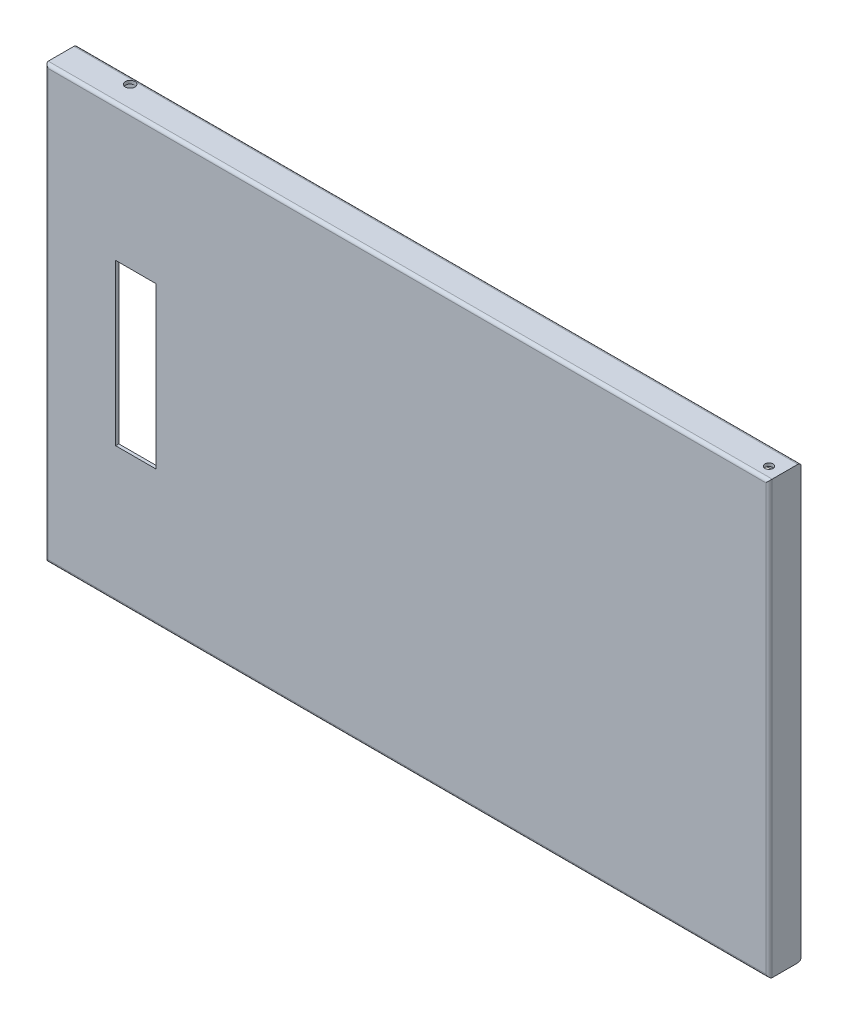
SolidWorks part; units mm, degrees
ref_plane "Front Plane" through (0, 0, 0) normal (0, 0, 1) x (1, 0, 0)
ref_plane "Top Plane" through (0, 0, 0) normal (0, 1, 0) x (1, 0, 0)
ref_plane "Right Plane" through (0, 0, 0) normal (1, 0, 0) x (0, 0, -1)
sketch "Sketch1" plane through (0, 0, 0) normal (0, 0, 1) x (1, 0, 0)
  line L1 (-225.5, 134.5) -> (225.5, 134.5)
  line L2 (-225.5, 134.5) -> (-225.5, -134.5)
  line L3 (-225.5, -134.5) -> (225.5, -134.5)
  line L4 (225.5, 134.5) -> (225.5, -134.5)
  line L5 (-225.5, 134.5) -> (225.5, -134.5) construction
  line L6 (-225.5, -134.5) -> (225.5, 134.5) construction
  point P0 (0, 0)
  dimension "D1" = 269
  dimension "D2" = 451
extrude "Boss-Extrude1" add sketch "Sketch1" along normal blind 20
shell "Shell1" thickness 11
sketch "Sketch2" plane through (0, 0, 9) normal (0, 0, -1) x (-1, 0, 0)
  line L1 (-214.5, 123.5) -> (214.5, 123.5)
  line L2 (-214.5, 123.5) -> (-214.5, -123.5)
  line L3 (-214.5, -123.5) -> (214.5, -123.5)
  line L4 (214.5, 123.5) -> (214.5, -123.5)
extrude "Cut-Extrude1" cut sketch "Sketch2" against normal blind 9
sketch "Sketch4" plane through (214.5, 0, 0) normal (-1, 0, 0) x (0, 0, 1)
  line L0 (18, -123.5) -> (0, -123.5) construction
  line L1 (18, 123.5) -> (2, 123.5)
  line L2 (18, 123.5) -> (18, -123.5)
  line L3 (18, -123.5) -> (2, -123.5)
  line L4 (2, 123.5) -> (2, -123.5)
  line L5 (0, -123.5) -> (0, 123.5) construction
  dimension "D1" = 2
extrude "Cut-Extrude3" cut sketch "Sketch4" against normal blind 9
sketch "Sketch8" plane through (0, 123.5, 0) normal (0, -1, 0) x (1, 0, 0)
  line L0 (-214.5, 18) -> (-214.5, 0) construction
  line L1 (223.5, 18) -> (-214.5, 18)
  line L2 (223.5, 18) -> (223.5, 2)
  line L3 (223.5, 2) -> (-214.5, 2)
  line L4 (-214.5, 18) -> (-214.5, 2)
  line L5 (214.5, 0) -> (-214.5, 0) construction
  dimension "D1" = 2
extrude "Cut-Extrude4" cut sketch "Sketch8" against normal blind 9
sketch "Sketch9" plane through (-214.5, 0, 0) normal (1, 0, 0) x (0, 0, -1)
  line L0 (-18, -123.5) -> (0, -123.5) construction
  line L1 (-18, 132.5) -> (-2, 132.5)
  line L2 (-18, 132.5) -> (-18, -123.5)
  line L3 (-18, -123.5) -> (-2, -123.5)
  line L4 (-2, 132.5) -> (-2, -123.5)
  line L5 (0, 123.5) -> (0, -123.5) construction
  dimension "D1" = 2
extrude "Cut-Extrude5" cut sketch "Sketch9" against normal blind 9
sketch "Sketch10" plane through (0, -123.5, 0) normal (0, 1, 0) x (1, 0, 0)
  line L0 (223.5, -2) -> (223.5, -18) construction
  line L1 (-223.5, -18) -> (223.5, -18)
  line L2 (-223.5, -18) -> (-223.5, -2)
  line L3 (-223.5, -2) -> (223.5, -2)
  line L4 (223.5, -18) -> (223.5, -2)
  line L5 (-214.5, 0) -> (214.5, 0) construction
  dimension "D1" = 2
extrude "Cut-Extrude6" cut sketch "Sketch10" against normal blind 9
sketch "Sketch11" plane through (0, 0, 20) normal (0, 0, 1) x (1, 0, 0)
  line L0 (-225.5, 134.5) -> (-225.5, -134.5) construction
  line L1 (-181.5, 50) -> (-156.5, 50)
  line L2 (-181.5, 50) -> (-181.5, -50)
  line L3 (-181.5, -50) -> (-156.5, -50)
  line L4 (-156.5, 50) -> (-156.5, -50)
  line L5 (225.5, 134.5) -> (-225.5, 134.5) construction
  point P8 (-156.5, 0)
  dimension "D1" = 69
  dimension "D2" = 25
  dimension "D3" = 100
  dimension "D4" = 134.5
extrude "Cut-Extrude7" cut sketch "Sketch11" against normal up to surface (2 mm away)
fillet "Fillet1" radius 2 8 edges at (0, -134.5, 0) (-225.5, 0, 0) (0, 134.5, 0) (223.5, 0, 2) (225.5, 0, 20) (0, -134.5, 20) (-225.5, 0, 20) (0, 134.5, 20)
fillet "Fillet2" radius 2 4 edges at (223.5, 0, 18) (0, -132.5, 18) (-223.5, 0, 18) (0, 132.5, 18)
sketch "Sketch12" plane through (0, 134.5, 0) normal (0, 1, 0) x (1, 0, 0)
  line L0 (-225.5, -18) -> (-225.5, -2) construction
  line L1 (-223.5, 0) -> (225.5, 0) construction
  circle A0 centre (-187.5, -5) radius 3
  dimension "D1" = 38
  dimension "D2" = 5
extrude "Cut-Extrude8" cut sketch "Sketch12" against normal up to surface (2 mm away) up to face at (44.3828, 132.5, 7.9172)
sketch "Sketch13" plane through (0, -134.5, 0) normal (0, -1, 0) x (1, 0, 0)
  line L0 (-225.5, 18) -> (-225.5, 2) construction
  line L1 (225.5, 0) -> (-223.5, 0) construction
  circle A0 centre (-150.5, 5) radius 4.3995
  dimension "D1" = 75
  dimension "D2" = 5
extrude "Cut-Extrude9" cut sketch "Sketch13" against normal up to surface (2 mm away) up to face at (44.3828, -132.5, 7.9172)
sketch "Sketch14" plane through (0, -134.5, 0) normal (0, -1, 0) x (1, 0, 0)
  line L0 (-223.5, 20) -> (223.5, 20) construction
  line L1 (225.5, 18) -> (225.5, 2) construction
  circle A0 centre (217.5, 12) radius 2.5
  dimension "D1" = 8
  dimension "D2" = 8
extrude "Cut-Extrude10" cut sketch "Sketch14" against normal through all
